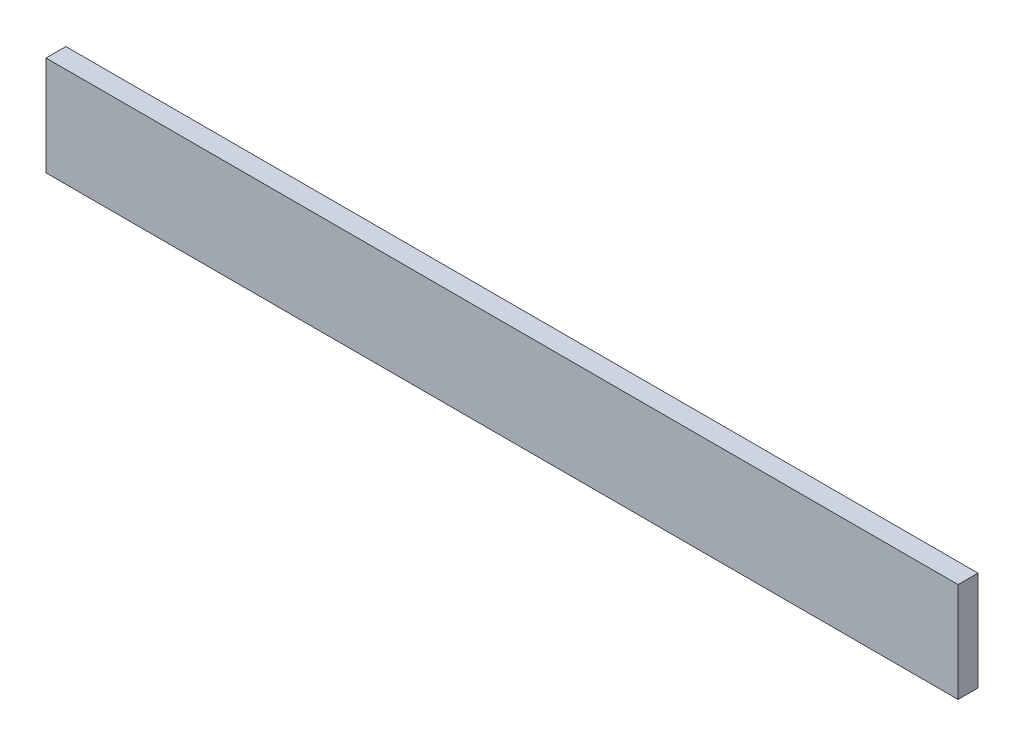
SolidWorks part; units mm, degrees
ref_plane "Спереди" through (0, 0, 0) normal (0, 0, 1) x (1, 0, 0)
ref_plane "Сверху" through (0, 0, 0) normal (0, 1, 0) x (1, 0, 0)
ref_plane "Справа" through (0, 0, 0) normal (1, 0, 0) x (0, 0, -1)
sketch "Эскиз1" plane through (0, 0, 0) normal (0, 0, 1) x (1, 0, 0)
  line L1 (0, 0) -> (458.4073, 0)
  line L2 (0, 0) -> (0, 50)
  line L3 (0, 50) -> (458.4073, 50)
  line L4 (458.4073, 0) -> (458.4073, 50)
extrude "Бобышка-Вытянуть1" add sketch "Эскиз1" along normal blind 10
